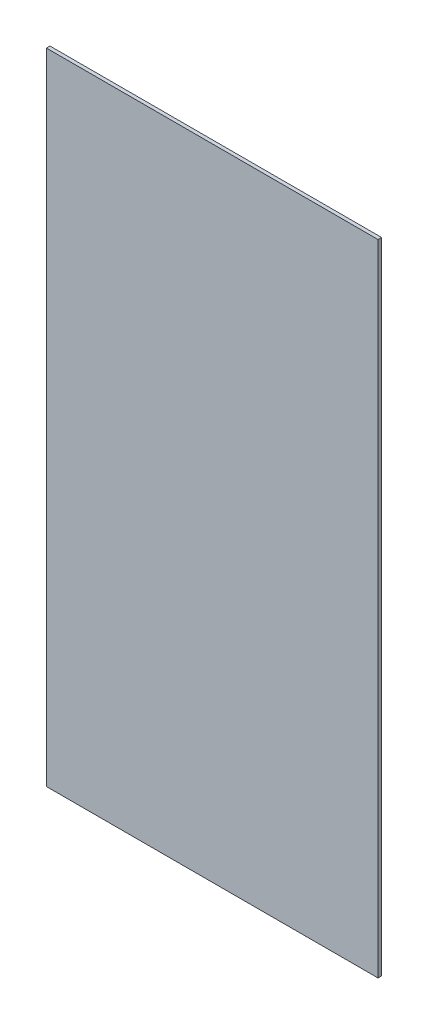
SolidWorks part; units mm, degrees
ref_plane "Plan de face" through (0, 0, 0) normal (0, 0, 1) x (1, 0, 0)
ref_plane "Plan de dessus" through (0, 0, 0) normal (0, 1, 0) x (1, 0, 0)
ref_plane "Plan de droite" through (0, 0, 0) normal (1, 0, 0) x (0, 0, -1)
sketch "Esquisse1" plane through (0, 0, 0) normal (0, 0, 1) x (1, 0, 0)
  line L0 (202.5709, -453.2994) -> (202.5709, 86.7006)
  line L1 (-77.4291, 86.7006) -> (202.5709, 86.7006)
  line L2 (-77.4291, 86.7006) -> (-77.4291, -453.2994)
  line L3 (-77.4291, -453.2994) -> (202.5709, -453.2994)
  dimension "D1" = 280
  dimension "D2" = 540
extrude "Boss.-Extru.1" add sketch "Esquisse1" along normal blind 3
equation "\"EpaisseurPlaque\"= 3"
equation "\"D1@Boss.-Extru.1\"=\"EpaisseurPlaque\""
equation "\"ProfondeurBoite\"=460"
equation "\"LongueurSyphon\"=270"
equation "\"LargeurSyphon\"=120"
equation "\"HauteurCoteDroit\"= 490"
equation "\"HauteurCoteGauche\"= 540"
equation "\"HauteurSolSyphon\"= 300"
equation "\"HauteurSyphon\"=\"HauteurCoteGauche\"-\"HauteurSolSyphon\""
equation "\"D2@Esquisse1\"= \"HauteurCoteGauche\""
equation "\"LargeurBoite\"= \"LargeurDroite\" + \"LargeurGauche\" + \"LargeurSyphon\""
equation "\"D1@Esquisse1\"= \"LargeurBoite\""
equation "\"LargeurDroite\"=10"
equation "\"LargeurGauche\"=150"
